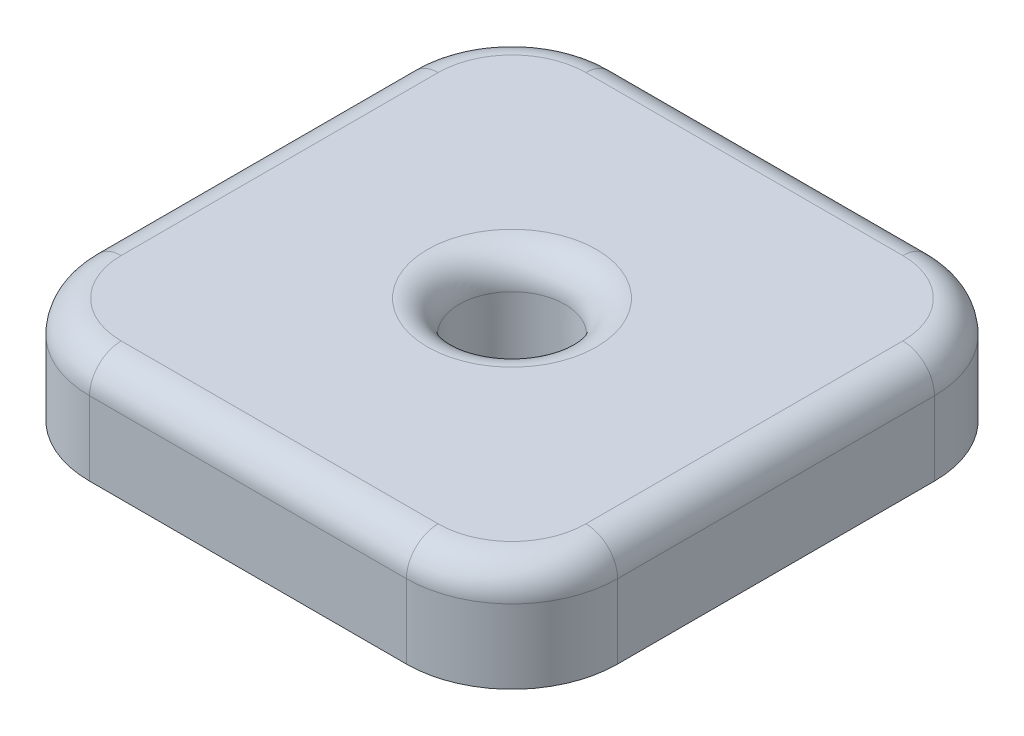
SolidWorks part; units mm, degrees
ref_plane "前视基准面" through (0, 0, 0) normal (0, 0, 1) x (1, 0, 0)
ref_plane "上视基准面" through (0, 0, 0) normal (0, 1, 0) x (1, 0, 0)
ref_plane "右视基准面" through (0, 0, 0) normal (1, 0, 0) x (0, 0, -1)
sketch "草图1" plane through (0, 0, 0) normal (0, 1, 0) x (1, 0, 0)
  line L1 (-25, -25) -> (25, -25)
  line L2 (-25, -25) -> (-25, 25)
  line L3 (-25, 25) -> (25, 25)
  line L4 (25, -25) -> (25, 25)
  line L5 (-25, -25) -> (25, 25) construction
  line L6 (-25, 25) -> (25, -25) construction
  point P0 (0, 0)
  dimension "D1" = 50
extrude "凸台-拉伸1" add sketch "草图1" along normal blind 10
fillet "圆角1" radius 10 4 edges at (-25, 5, 25) (-25, 5, -25) (25, 5, -25) (25, 5, 25)
sketch "草图2" plane through (0, 10, 0) normal (0, 1, 0) x (1, 0, 0)
  circle A0 centre (0, 0) radius 5
  point P2 (0, 0)
  dimension "D1" = 10
extrude "切除-拉伸1" cut sketch "草图2" against normal blind 10
fillet "圆角2" radius 3 9 edges at (-22.0711, 10, -22.0711) (0, 10, -25) (22.0711, 10, -22.0711) (25, 10, 0) (22.0711, 10, 22.0711) (0, 10, 25) (-22.0711, 10, 22.0711) (-25, 10, 0) (0, 10, 5)
